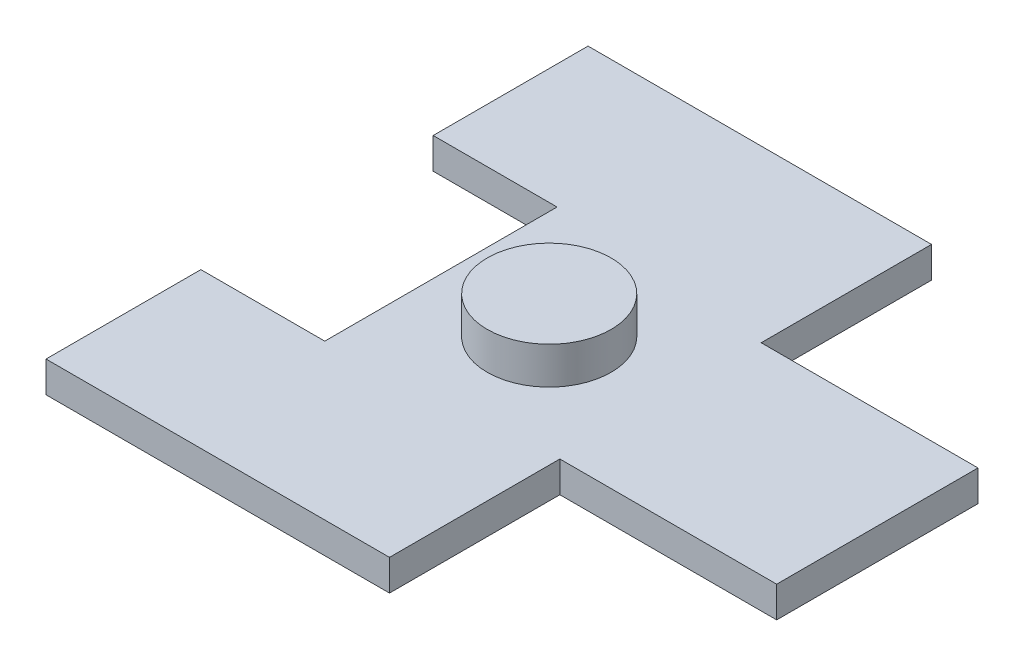
SolidWorks part; units mm, degrees
ref_plane "Front Plane" through (0, 0, 0) normal (0, 0, 1) x (1, 0, 0)
ref_plane "Top Plane" through (0, 0, 0) normal (0, 1, 0) x (1, 0, 0)
ref_plane "Right Plane" through (0, 0, 0) normal (1, 0, 0) x (0, 0, -1)
sketch "Sketch1" plane through (0, 0, 0) normal (0, 1, 0) x (1, 0, 0)
  line L0 (0.6248, 6.5) -> (0.6248, 17.5)
  line L1 (-9.4168, -17.5) -> (0.6248, -17.5)
  line L2 (-13.5552, -7.5) -> (-13.5552, 7.5)
  line L3 (-9.4168, 17.5) -> (0.6248, 17.5)
  line L4 (0.6248, -17.5) -> (0.6248, -6.5)
  line L5 (-9.4168, 17.5) -> (-21.5552, 17.5)
  line L7 (-13.5552, 7.5) -> (-21.5552, 7.5)
  line L8 (-21.5552, 17.5) -> (-21.5552, 7.5)
  line L9 (-9.4168, -17.5) -> (-21.5552, -17.5)
  line L11 (-13.5552, -7.5) -> (-21.5552, -7.5)
  line L12 (-21.5552, -17.5) -> (-21.5552, -7.5)
  line L13 (0.6248, 6.5) -> (14.6248, 6.5)
  line L15 (0.6248, -6.5) -> (14.6248, -6.5)
  line L16 (14.6248, 6.5) -> (14.6248, -6.5)
  point P0 (0, 0)
  dimension "D1" = 35
  dimension "D2" = 10
  dimension "D3" = 8
  dimension "D4" = 22.18
  dimension "D5" = 11
  dimension "D6" = 14
extrude "Boss-Extrude1" add sketch "Sketch1" along normal blind 2
sketch "Sketch2" plane through (0, 2, 0) normal (0, 1, 0) x (1, 0, 0)
  line L0 (-23.4997, 0) -> (10.8439, 0) construction
  line L1 (-13.5552, 7.5) -> (-13.5552, -7.5) construction
  circle A0 centre (-6.5639, 0) radius 4
  dimension "D2" = 8
  dimension "D1" = 6.9913
extrude "Boss-Extrude2" add sketch "Sketch2" along normal blind 2.4
